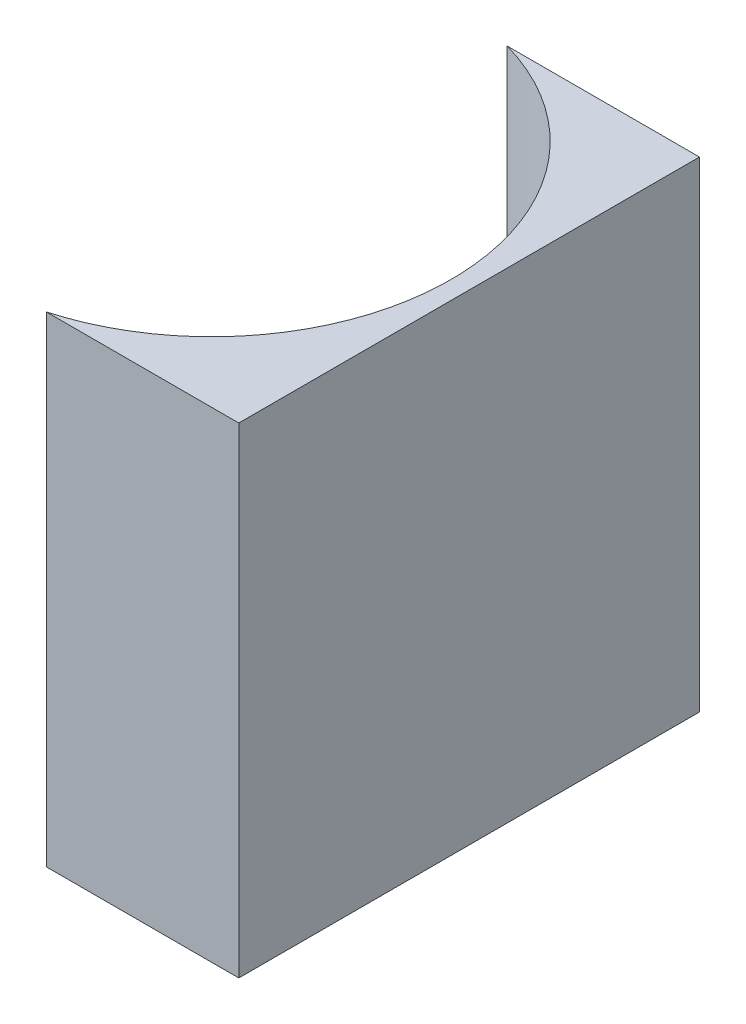
SolidWorks part; units mm, degrees
ref_plane "前视基准面" through (0, 0, 0) normal (0, 0, 1) x (1, 0, 0)
ref_plane "上视基准面" through (0, 0, 0) normal (0, 1, 0) x (1, 0, 0)
ref_plane "右视基准面" through (0, 0, 0) normal (1, 0, 0) x (0, 0, -1)
sketch "草图1" plane through (0, 0, 0) normal (0, 1, 0) x (1, 0, 0)
  line L0 (0, 0) -> (0, -50.8)
  line L1 (0, 0) -> (-21.2028, 0)
  line L2 (0, -50.8) -> (-21.2028, -50.8)
  line L3 (8.2336, -25.4) -> (-10.4405, -25.4) construction
  arc A0 (-21.2028, -50.8) -> (-21.2028, 0) centre (-28.4, -25.4) ccw
  point P7 (-2, -25.4)
  point P8 (0, -25.4)
  dimension "D2" = 26.4
  dimension "D3" = 2
  dimension "D1" = 50.8
extrude "凸台-拉伸1" add sketch "草图1" along normal blind 53
